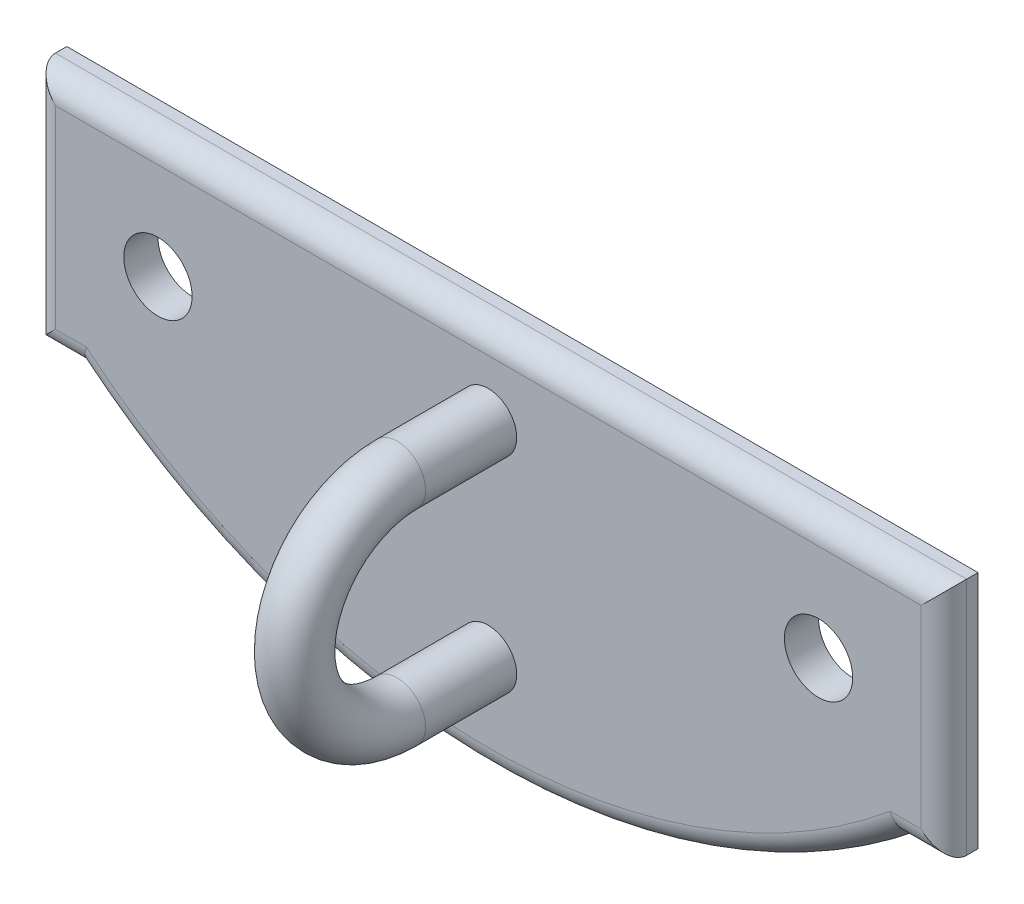
SolidWorks part; units mm, degrees
material "1060 Alloy"
ref_plane "Front" through (0, 0, 0) normal (0, 0, 1) x (1, 0, 0)
ref_plane "Top" through (0, 0, 0) normal (0, 1, 0) x (1, 0, 0)
ref_plane "Right" through (0, 0, 0) normal (1, 0, 0) x (0, 0, -1)
sketch "Sketch1" plane through (0, 0, 0) normal (0, 0, 1) x (1, 0, 0)
  line L0 (0, 0) -> (20, 0)
  line L1 (55, 0) -> (-55, 0) construction
  line L2 (20, 0) -> (20, -10.5)
  line L3 (20, -10.5) -> (18, -10.5)
  line L4 (0, 0) -> (-20, 0)
  line L5 (-20, 0) -> (-20, -10.5)
  line L6 (-20, -10.5) -> (-18, -10.5)
  arc A1 (18, -10.5) -> (-18, -10.5) centre (0, 11.5706) cw
  dimension "D7" = 28.48
  dimension "D1" = 20
  dimension "D2" = 20
  dimension "D3" = 2
  dimension "D4" = 2
  dimension "D5" = 10.5
  dimension "D6" = 10.5
extrude "Boss-Extrude1" add sketch "Sketch1" along normal blind 1.5
sketch "Sketch2" plane through (0, 0, 1.5) normal (0, 0, 1) x (1, 0, 0)
  line L0 (-20, 0) -> (-20, -10.5) construction
  line L1 (0.825, 0) -> (-0.825, 0) construction
  line L2 (0, -0.825) -> (0, 0.825) construction
  circle A0 centre (-14.5, -5.25) radius 1.5
  circle A1 centre (14.5, -5.25) radius 1.5
  dimension "D1" = 5.5
  dimension "D3" = 3
  dimension "D2" = 5.25
extrude "Cut-Extrude1" cut sketch "Sketch2" against normal blind 1.5
sketch "Sketch3" plane through (0, 0, 1.5) normal (0, 0, 1) x (1, 0, 0)
  line L0 (0, -0.825) -> (0, 0.825) construction
  line L1 (0.825, 0) -> (-0.825, 0) construction
  circle A1 centre (0, -12.5) radius 1.25
  dimension "D2" = 2.5
  dimension "D4" = 12.5
sketch "Sketch4" plane through (0, 0, 0) normal (1, 0, 0) x (0, 0, -1)
  line L0 (-5.5, -3.5) -> (-1.5, -3.5)
  line L1 (-1.5, -12.5) -> (-5.5, -12.5)
  line L4 (-1.5, -3.75) -> (-1.5, -6.75) construction
  arc A0 (-5.5, -12.5) -> (-5.5, -3.5) centre (-5.5, -8) cw
  dimension "D1" = 4
  dimension "D2" = 9
sweep "Sweep2" add profiles "Sketch3" path "Sketch4"
fillet "Fillet1" radius 1 6 edges at (0, 0, 1.5) (20, -5.25, 1.5) (19, -10.5, 1.5) (0, -16.9094, 1.5) (-19, -10.5, 1.5) (-20, -5.25, 1.5)
